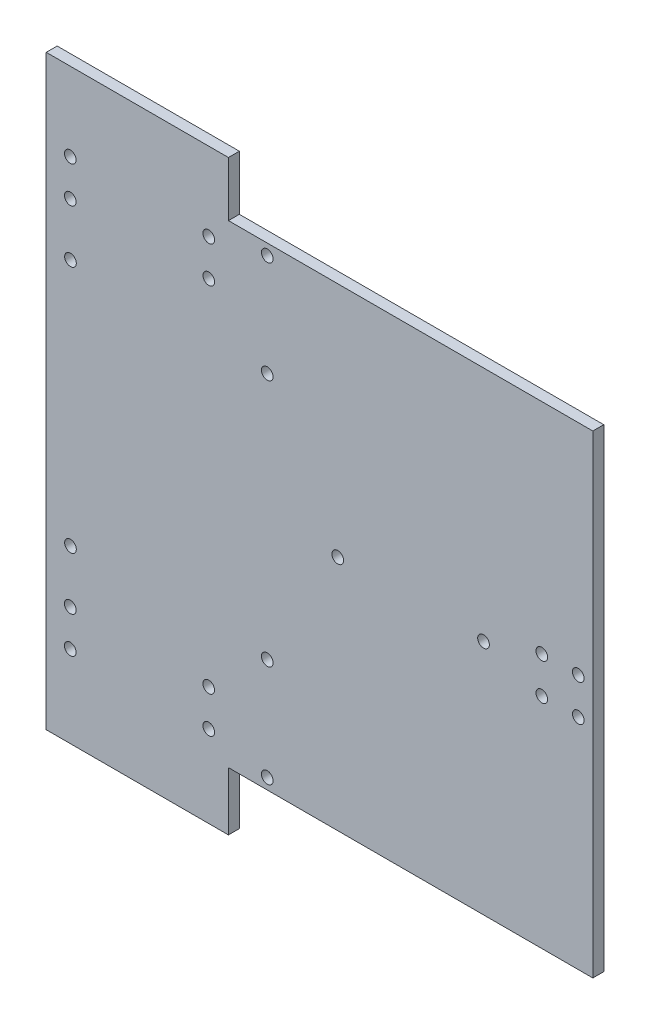
SolidWorks part; units mm, degrees
ref_plane "Front Plane" through (0, 0, 0) normal (0, 0, 1) x (1, 0, 0)
ref_plane "Top Plane" through (0, 0, 0) normal (0, 1, 0) x (1, 0, 0)
ref_plane "Right Plane" through (0, 0, 0) normal (1, 0, 0) x (0, 0, -1)
sketch "Sketch1" plane through (0, 0, 0) normal (0, 0, 1) x (1, 0, 0)
  line L1 (-75, -65) -> (75, -65)
  line L2 (-75, -65) -> (-75, 65)
  line L3 (-75, 65) -> (75, 65)
  line L4 (75, -65) -> (75, 65)
  line L5 (-75, -65) -> (75, 65) construction
  line L6 (-75, 65) -> (75, -65) construction
  point P0 (0, 0)
  dimension "D1" = 150
  dimension "D2" = 130
extrude "Boss-Extrude1" add sketch "Sketch1" along normal blind 3
sketch "Sketch3" plane through (0, 0, 0) normal (0, 0, -1) x (-1, 0, 0)
  line L0 (75, 65) -> (75, 80)
  line L1 (75, 80) -> (25, 80)
  line L2 (25, 80) -> (25, 65)
  line L3 (-75, 65) -> (75, 65) construction
  line L4 (75, -65) -> (75, -81)
  line L5 (75, -81) -> (25, -81)
  line L6 (25, -81) -> (25, -65)
  line L7 (75, -65) -> (-75, -65) construction
  line L8 (25, 65) -> (75, 65)
  line L9 (25, -65) -> (75, -65)
  dimension "D1" = 50
  dimension "D2" = 15
  dimension "D3" = 50
  dimension "D4" = 16
extrude "Boss-Extrude2" add sketch "Sketch3" against normal blind 3
sketch "Sketch2" plane through (0, 0, 3) normal (0, 0, 1) x (1, 0, 0)
  line L0 (-75, 80) -> (-75, -81) construction
  line L1 (75, 65) -> (-25, 65) construction
  line L2 (75, 65) -> (-25, 65) construction
  line L3 (0, 0) -> (75, 0) construction
  line L4 (75, -65) -> (75, 65) construction
  line L5 (-13, 62) -> (-13, 3.4) construction
  line L6 (-13, 3.4) -> (-60.3, 3.4) construction
  line L7 (-60.3, 3.4) -> (-60.3, 62) construction
  line L8 (-60.3, 62) -> (-13, 62) construction
  line L9 (0, 0) -> (-282.0509, 0) construction
  line L10 (-36.65, 3.4) -> (-36.65, 62) construction
  line L11 (-13, 32.7) -> (-60.3, 32.7) construction
  line L12 (11.576, 53.5) -> (-92.9014, 53.5) construction
  line L13 (55, -65) -> (55, 65) construction
  line L17 (-25, -65) -> (75, -65) construction
  circle A15 centre (-30.4, 58.5) radius 1.6
  circle A16 centre (-68.4, 58.5) radius 1.6
  circle A17 centre (-68.4, 48.5) radius 1.6
  circle A18 centre (-30.4, 48.5) radius 1.6
  circle A19 centre (-68.4, -48.5) radius 1.6
  circle A20 centre (-68.4, -58.5) radius 1.6
  circle A21 centre (-30.4, -58.5) radius 1.6
  circle A22 centre (-30.4, -48.5) radius 1.6
  circle A23 centre (71, -5) radius 1.6
  circle A24 centre (71, 5) radius 1.6
  circle A25 centre (61, -5) radius 1.6
  circle A26 centre (61, 5) radius 1.6
  circle A27 centre (-68.35, -34) radius 1.6
  circle A28 centre (-14.35, -34) radius 1.6
  circle A29 centre (-14.35, -62) radius 1.6
  circle A30 centre (-14.35, 62) radius 1.6
  circle A31 centre (-14.35, 34) radius 1.6
  circle A32 centre (-68.35, 34) radius 1.6
  circle A33 centre (45, 0) radius 1.6
  circle A34 centre (5, 0) radius 1.6
  dimension "D4" = 6.6
  dimension "D5" = 3
  dimension "D6" = 3.2
  dimension "D9" = 3.2
  dimension "D15" = 5
  dimension "D20" = 10
  dimension "D25" = 54
  dimension "D28" = 3.2
  dimension "D29" = 3.2
  dimension "D33" = 31
  dimension "D34" = 3.2
  dimension "D36" = 28
  dimension "D7" = 3.2
  dimension "D8" = 3.2
  dimension "D21" = 3.2
  dimension "D35" = 3.2
  dimension "D37" = 54
  dimension "D38" = 3.2
  dimension "D39" = 3.2
  dimension "D10" = 4
  dimension "D11" = 5
  dimension "D12" = 4
  dimension "D13" = 5
  dimension "D14" = 5
  dimension "D16" = 10
  dimension "D17" = 10
  dimension "D18" = 6
  dimension "D19" = 58.6
  dimension "D22" = 47.3
  dimension "D23" = 6.65
  dimension "D24" = 31
  dimension "D26" = 6.25
  dimension "D27" = 38
  dimension "D30" = 6.5
  dimension "D31" = 6.5
  dimension "D32" = 5
  dimension "D40" = 40
extrude "Cut-Extrude1" cut sketch "Sketch2" against normal blind 10
equation "\"30э\"=3"
